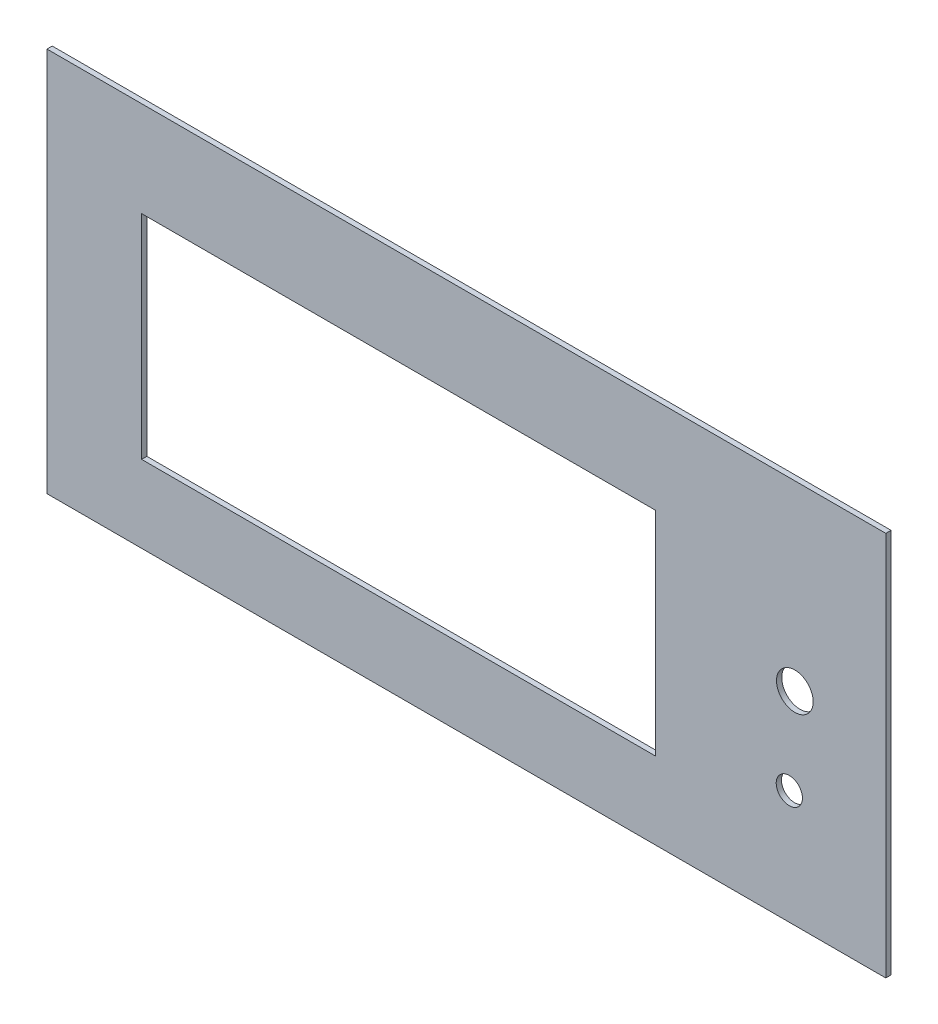
SolidWorks part; units mm, degrees
ref_plane "Płaszczyzna przednia" through (0, 0, 0) normal (0, 0, 1) x (1, 0, 0)
ref_plane "Płaszczyzna górna" through (0, 0, 0) normal (0, 1, 0) x (1, 0, 0)
ref_plane "Płaszczyzna prawa" through (0, 0, 0) normal (1, 0, 0) x (0, 0, -1)
sketch "Szkic1" plane through (0, 0, 0) normal (0, 0, 1) x (1, 0, 0)
  line L4 (36.6, 14.3) -> (-61.4, 14.3)
  line L5 (36.6, -26.3) -> (36.6, 14.3)
  line L6 (-61.4, -26.3) -> (36.6, -26.3)
  line L7 (-61.4, 14.3) -> (-61.4, -26.3)
  line L8 (36.6, 14.3) -> (-61.4, 14.3)
  line L9 (36.6, -26.3) -> (36.6, 14.3)
  line L10 (-61.4, -26.3) -> (36.6, -26.3)
  line L11 (-61.4, 14.3) -> (-61.4, -26.3)
  line L12 (80.5461, 32.4548) -> (-79.4539, 32.4548)
  line L13 (80.5461, -41) -> (80.5461, 32.4548)
  line L14 (-79.4539, -41) -> (80.5461, -41)
  line L15 (-79.4539, 32.4548) -> (-79.4539, -41)
  line L16 (80.5461, 32.4548) -> (-79.4539, 32.4548)
  line L17 (80.5461, -41) -> (80.5461, 32.4548)
  line L18 (-79.4539, -41) -> (80.5461, -41)
  line L19 (-79.4539, 32.4548) -> (-79.4539, -41)
  circle A1 centre (62.1461, -19.2452) radius 2.5
  circle A2 centre (62.1461, -19.2452) radius 2.5
  circle A3 centre (63.1961, -2.2952) radius 3.5
  circle A4 centre (63.1961, -2.2952) radius 3.5
  dimension "D1" = 0
  dimension "D2" = 0
  dimension "D3" = 0
  dimension "D4" = 0
extrude "Dodanie-wyciągnięcie1" add sketch "Szkic1" along normal blind 1
ref_plane "Płaszczyzna3" through (50, 0, 0) normal (1, 0, 0) x (0, 0, -1)
sketch "Szkic18" plane through (50, 0, 0) normal (1, 0, 0) x (0, 0, -1)
  line L0 (22.0863, -7.4603) -> (36.7302, 18.1768)
  point P2 (36.7302, 18.1768)
